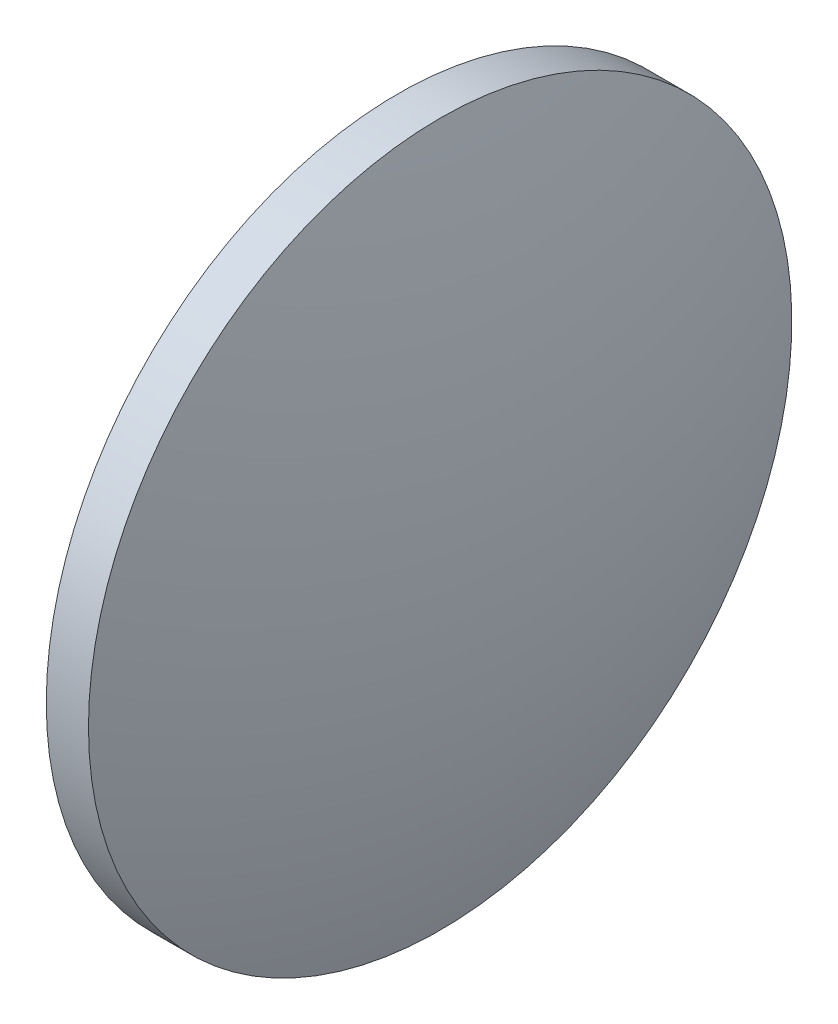
SolidWorks part; units mm, degrees
ref_plane "前视基准面" through (0, 0, 0) normal (0, 0, 1) x (1, 0, 0)
ref_plane "上视基准面" through (0, 0, 0) normal (0, 1, 0) x (1, 0, 0)
ref_plane "右视基准面" through (0, 0, 0) normal (1, 0, 0) x (0, 0, -1)
sketch "草图1" plane through (0, 0, 0) normal (0, 0, 1) x (1, 0, 0)
  line L0 (487.7863, 116.2375) -> (509.7624, 116.2375) construction
  line L1 (491.7581, 116.2375) -> (491.7581, 141.2375)
  line L2 (491.7581, 141.2375) -> (494.7581, 141.2375)
  line L3 (498.6281, 116.2375) -> (491.7581, 116.2375)
  arc A0 (498.6281, 116.2375) -> (494.7581, 141.2375) centre (415.9437, 116.2375) ccw
revolve "旋转1" add sketch "草图1" angle 360 about L0
